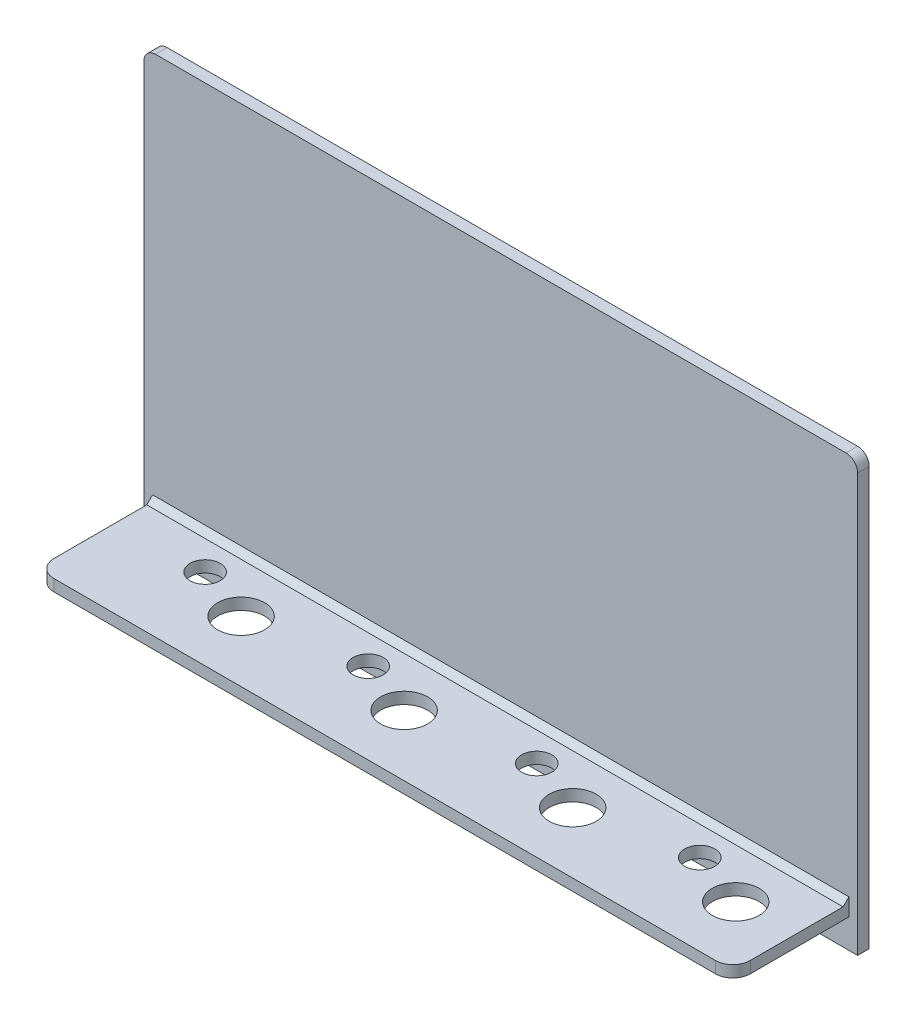
SolidWorks part; units mm, degrees
ref_plane "Plan de face" through (0, 0, 0) normal (0, 0, 1) x (1, 0, 0)
ref_plane "Plan de dessus" through (0, 0, 0) normal (0, 1, 0) x (1, 0, 0)
ref_plane "Plan de droite" through (0, 0, 0) normal (1, 0, 0) x (0, 0, -1)
sketch "Esquisse2" plane through (0, 0, 0) normal (0, 0, 1) x (1, 0, 0)
  line L1 (-61.5, -37) -> (61.5, -37)
  line L2 (-61.5, -37) -> (-61.5, 37)
  line L3 (-61.5, 37) -> (61.5, 37)
  line L4 (61.5, -37) -> (61.5, 37)
  line L5 (-61.5, -37) -> (61.5, 37) construction
  line L6 (-61.5, 37) -> (61.5, -37) construction
  point P0 (0, 0)
  dimension "D1" = 123
  dimension "D2" = 74
extrude "Boss.-Extru.1" add sketch "Esquisse2" along normal blind 2
sketch "Esquisse3" plane through (0, 0, 2) normal (0, 0, 1) x (1, 0, 0)
  line L0 (0, -31) -> (0, 0) construction
  line L1 (60, -30) -> (-60, -30)
  line L2 (60, -30) -> (60, -32)
  line L3 (60, -32) -> (-60, -32)
  line L4 (-60, -30) -> (-60, -32)
  line L5 (60, -30) -> (-60, -32) construction
  line L6 (60, -32) -> (-60, -30) construction
  line L8 (-61.5, -37) -> (61.5, -37) construction
  point P0 (0, -31)
  dimension "D1" = 2
  dimension "D2" = 120
  dimension "D3" = 5
extrude "Boss.-Extru.2" add sketch "Esquisse3" along normal blind 20
sketch "Esquisse4" plane through (0, -32, 0) normal (0, -1, 0) x (1, 0, 0)
  line L0 (-60, 2) -> (60, 2) construction
  line L1 (60, 22) -> (60, 2) construction
  circle A0 centre (50, 11.5) radius 4.05
  circle A1 centre (40.3, 8) radius 2.6
  dimension "D1" = 8.1
  dimension "D2" = 5.2
  dimension "D3" = 9.5
  dimension "D4" = 10
  dimension "D5" = 6
  dimension "D6" = 9.7
extrude "Enlèv. mat.-Extru.1" cut sketch "Esquisse4" against normal through all
pattern_linear "Répétition linéaire1" count 2 spacing 28.1 along (-1, 0, 0) of "Enlèv. mat.-Extru.1"
pattern_linear "Répétition linéaire2" count 2 spacing 57.15 along (-1, 0, 0) of "Répétition linéaire1", "Enlèv. mat.-Extru.1"
fillet "Congé1" radius 3 2 edges at (-60, -31, 22) (60, -31, 22)
sketch "Esquisse5" plane through (0, -32, 0) normal (0, -1, 0) x (1, 0, 0)
  line L0 (-54.65, 11.5) -> (-35.25, 11.5) construction
  line L1 (-44.95, 8) -> (-44.95, 11.5) construction
  line L2 (-26.55, 11.5) -> (-7.15, 11.5) construction
  line L3 (40.3, 11.5) -> (40.3, 8) construction
  line L4 (2.5, 11.5) -> (21.9, 11.5) construction
  line L6 (30.6, 11.5) -> (50, 11.5) construction
  line L7 (12.2, 11.5) -> (12.2, 8) construction
  line L9 (-16.85, 11.5) -> (-16.85, 8) construction
  circle A0 centre (-35.25, 11.5) radius 4.05 construction
  circle A1 centre (-7.15, 11.5) radius 4.05 construction
  circle A2 centre (21.9, 11.5) radius 4.05 construction
  circle A4 centre (50, 11.5) radius 4.05 construction
  circle A5 centre (-16.85, 8) radius 2.6 construction
  circle A6 centre (12.2, 8) radius 2.6 construction
  circle A7 centre (40.3, 8) radius 2.6 construction
  text T0 "<b>1</b>" font "Century Gothic" height 8
  text T1 "<b>2</b>" font "Century Gothic" height 8
  text T2 "<b>3</b>" font "Century Gothic" height 8
  text T3 "<b>4</b>" font "Century Gothic" height 8
  point P21 (0, 0)
  point P27 (0, 0)
  point P30 (0, 0)
  point P33 (0, 0)
extrude "Enlèv. mat.-Extru.2" cut sketch "Esquisse5" against normal blind 0.5
fillet "Congé2" radius 2 2 edges at (61.5, 37, 1) (-61.5, 37, 1)
chamfer "Chanfrein1" distance 1 angle 45 1 edges at (0, -30, 2)
